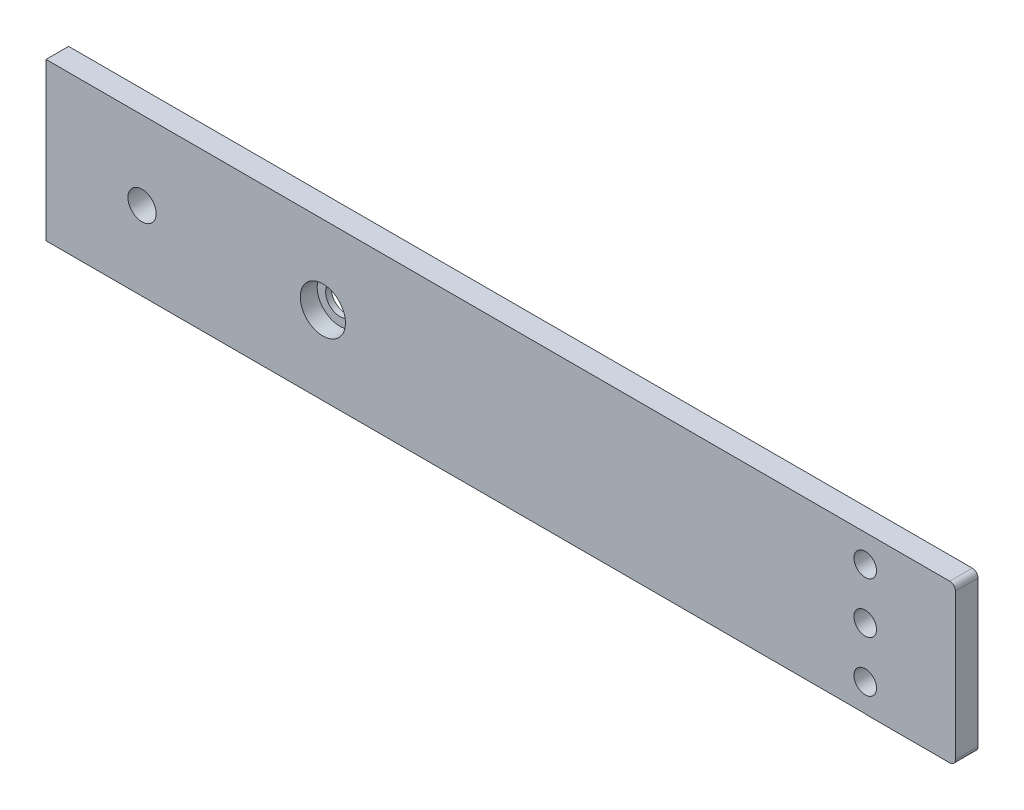
SolidWorks part; units mm, degrees
ref_plane "前视基准面" through (0, 0, 0) normal (0, 0, 1) x (1, 0, 0)
ref_plane "上视基准面" through (0, 0, 0) normal (0, 1, 0) x (1, 0, 0)
ref_plane "右视基准面" through (0, 0, 0) normal (1, 0, 0) x (0, 0, -1)
sketch "草图1" plane through (0, 0, 0) normal (0, 0, 1) x (1, 0, 0)
  line L0 (-75.5387, 0) -> (52.4613, 0) construction
  line L1 (-75.5387, 13.9) -> (52.4613, 13.9)
  line L2 (-75.5387, -13.9) -> (52.4613, -13.9)
  line L3 (-75.5387, 13.9) -> (-92.5387, 13.9)
  line L4 (-92.5387, 13.9) -> (-92.5387, -13.9)
  line L5 (-92.5387, -13.9) -> (-75.5387, -13.9)
  line L6 (52.4613, -13.9) -> (52.4613, -13.95)
  line L7 (52.4613, 13.9) -> (65.4221, 13.9)
  line L9 (52.4613, -13.95) -> (67.4221, -13.95)
  line L10 (68.4221, 10.9) -> (68.4221, -12.95)
  line L12 (65.4221, 13.9) -> (67.4221, 13.9)
  line L15 (68.4221, 12.9) -> (68.4221, 10.9)
  circle A2 centre (-75.5387, 0) radius 2.5
  circle A3 centre (52.4613, 0) radius 2
  circle A4 centre (-43.5387, 0) radius 2.5
  arc A6 (68.4221, -12.95) -> (67.4221, -13.95) centre (67.4221, -12.95) cw
  arc A7 (67.4221, 13.9) -> (68.4221, 12.9) centre (67.4221, 12.9) cw
  point P3 (2.4613, 0)
  dimension "D1" = 128
  dimension "D2" = 4
  dimension "D3" = 5
  dimension "D4" = 1
  dimension "D5" = 5
  dimension "D6" = 32
  dimension "D7" = 17
extrude "凸台-拉伸1" add sketch "草图1" along normal blind 4
sketch "草图2" plane through (0, 0, 0) normal (0, 0, -1) x (-1, 0, 0)
  circle A0 centre (-52.4613, -9) radius 2
  circle A1 centre (-52.4613, 0) radius 2 construction
  circle A2 centre (-52.4613, 9) radius 2
  dimension "D1" = 4
  dimension "D2" = 9
  dimension "D3" = 4
  dimension "D4" = 9
extrude "切除-拉伸1" cut sketch "草图2" against normal blind 10
sketch "草图4" plane through (0, 0, 4) normal (0, 0, 1) x (1, 0, 0)
  circle A0 centre (-43.5387, 0) radius 4
  dimension "D1" = 8
extrude "切除-拉伸2" cut sketch "草图4" against normal blind 3
